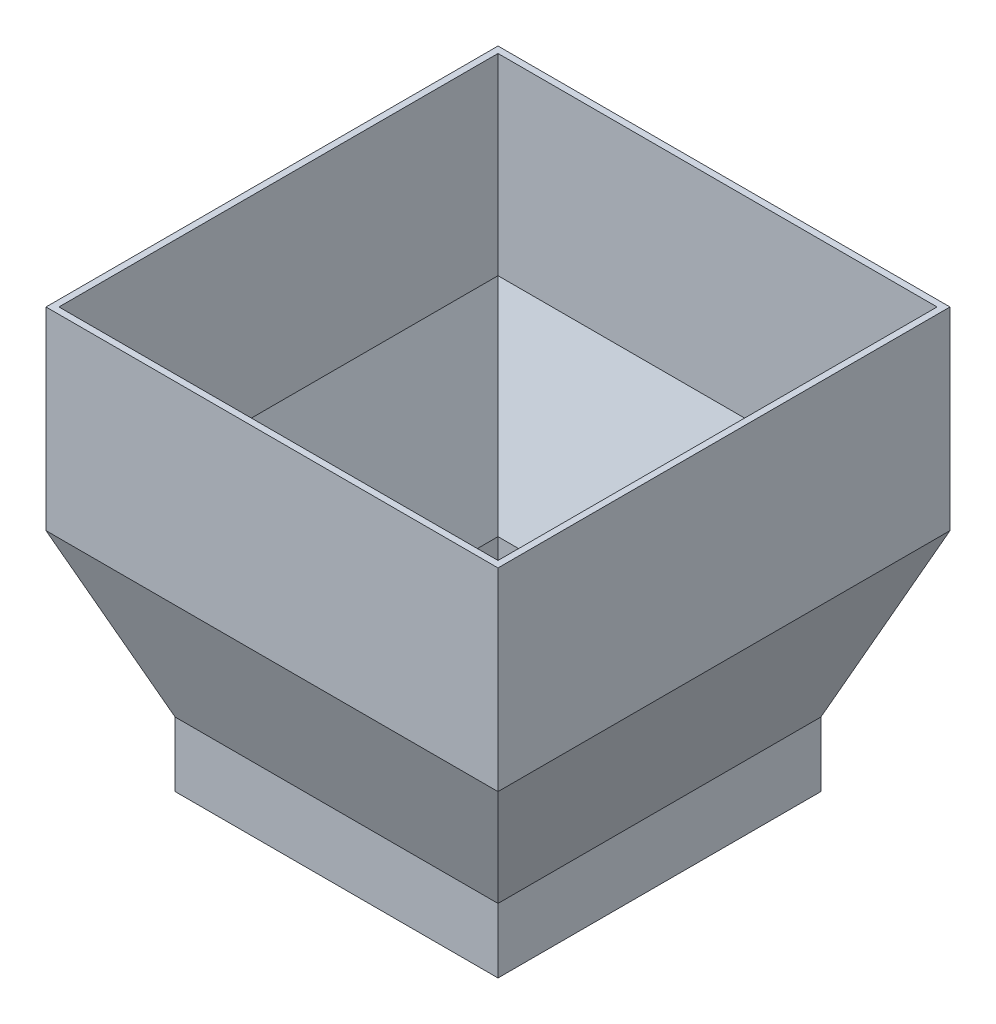
SolidWorks part; units mm, degrees
ref_plane "Front Plane" through (0, 0, 0) normal (0, 0, 1) x (1, 0, 0)
ref_plane "Top Plane" through (0, 0, 0) normal (0, 1, 0) x (1, 0, 0)
ref_plane "Right Plane" through (0, 0, 0) normal (1, 0, 0) x (0, 0, -1)
sketch "Sketch1" plane through (0, 0, 0) normal (0, 1, 0) x (1, 0, 0)
  line L1 (-350, 350) -> (350, 350)
  line L2 (-350, 350) -> (-350, -350)
  line L3 (-350, -350) -> (350, -350)
  line L4 (350, 350) -> (350, -350)
  line L5 (-350, 350) -> (350, -350) construction
  line L6 (-350, -350) -> (350, 350) construction
  point P0 (0, 0)
  dimension "D1" = 700
  dimension "D2" = 700
extrude "Boss-Extrude1" add sketch "Sketch1" along normal blind 300
ref_plane "Plane1" through (0, -250, 0) normal (0, -1, 0) x (-1, 0, 0)
sketch "Sketch2" plane through (0, -250, 0) normal (0, -1, 0) x (-1, 0, 0)
  line L1 (-250, -250) -> (250, -250)
  line L2 (-250, -250) -> (-250, 250)
  line L3 (-250, 250) -> (250, 250)
  line L4 (250, -250) -> (250, 250)
  line L5 (-250, -250) -> (250, 250) construction
  line L6 (-250, 250) -> (250, -250) construction
  point P0 (0, 0)
  dimension "D1" = 500
  dimension "D2" = 500
loft "Loft1" add profiles "Sketch2" section face at (0, 0, 0) section "Sketch2"
sketch "Sketch3" plane through (0, -250, 0) normal (0, -1, 0) x (1, 0, 0)
  line L1 (-250, 250) -> (250, 250)
  line L2 (-250, 250) -> (-250, -250)
  line L3 (-250, -250) -> (250, -250)
  line L4 (250, 250) -> (250, -250)
  line L5 (-250, 250) -> (250, -250) construction
  line L6 (-250, -250) -> (250, 250) construction
  point P0 (0, 0)
extrude "Boss-Extrude2" add sketch "Sketch3" along normal blind 100
shell "Shell1" thickness 10
